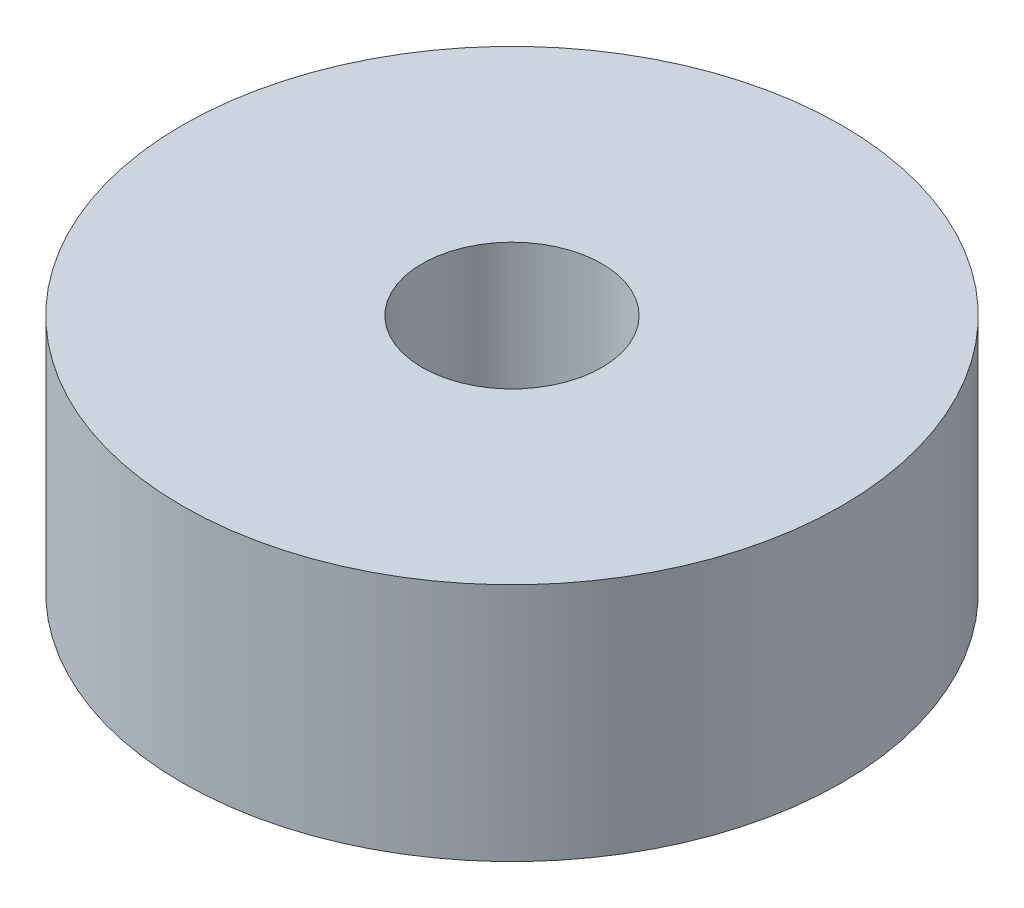
SolidWorks part; units mm, degrees
ref_plane "Front Plane" through (0, 0, 0) normal (0, 0, 1) x (1, 0, 0)
ref_plane "Top Plane" through (0, 0, 0) normal (0, 1, 0) x (1, 0, 0)
ref_plane "Right Plane" through (0, 0, 0) normal (1, 0, 0) x (0, 0, -1)
sketch "Sketch1" plane through (0, 0, 0) normal (0, 1, 0) x (1, 0, 0)
  circle A0 centre (0, 0) radius 1.5
  circle A1 centre (0, 0) radius 5.5
  dimension "D1" = 4
  dimension "D2" = 3
extrude "Boss-Extrude1" add sketch "Sketch1" along normal blind 4
